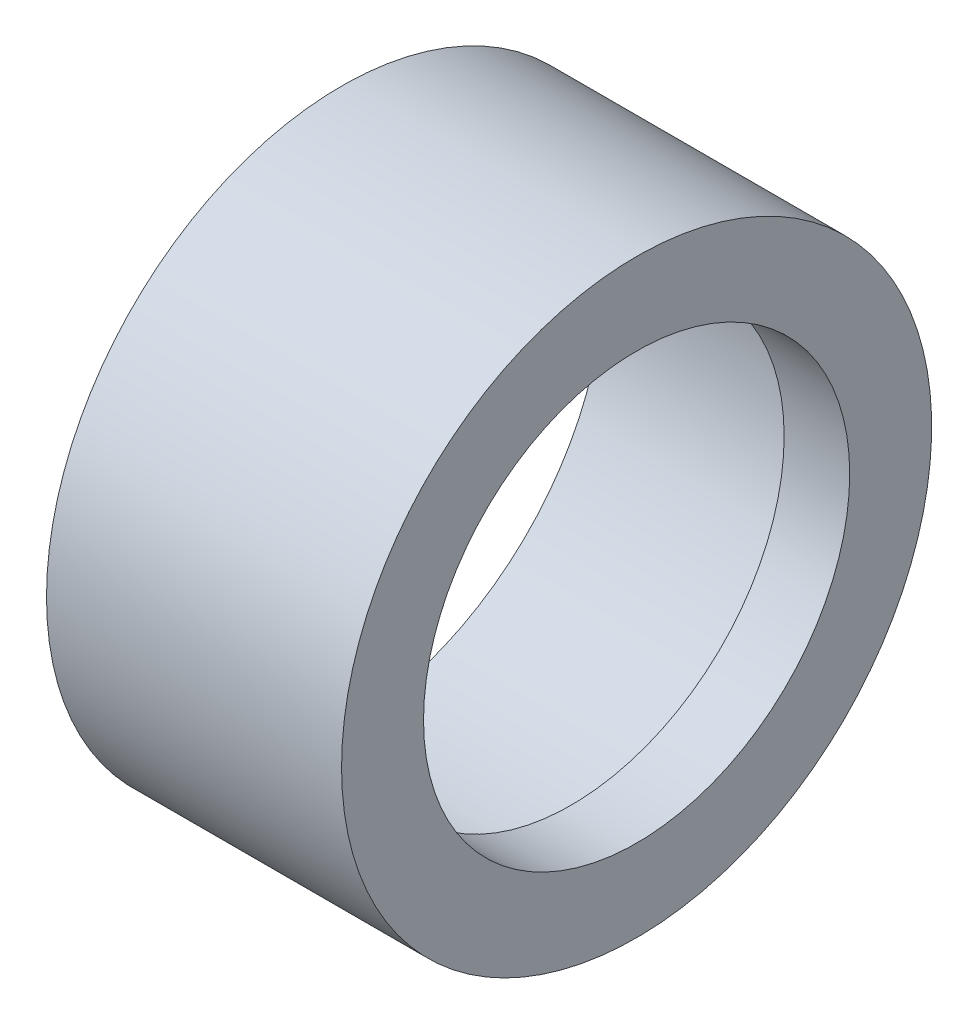
SolidWorks part; units mm, degrees
material "AISI Тип 316L нержавеющая сталь"
ref_plane "Спереди" through (0, 0, 0) normal (0, 0, 1) x (1, 0, 0)
ref_plane "Сверху" through (0, 0, 0) normal (0, 1, 0) x (1, 0, 0)
ref_plane "Справа" through (0, 0, 0) normal (1, 0, 0) x (0, 0, -1)
sketch "Эскиз1" plane through (0, 0, 0) normal (0, 0, 1) x (1, 0, 0)
  line L0 (0, 4) -> (3.5, 4)
  line L1 (3.5, 4) -> (3.5, 3.25)
  line L2 (3.5, 3.25) -> (4.5, 3.25)
  line L3 (4.5, 3.25) -> (4.5, 4.5)
  line L4 (4.5, 4.5) -> (0, 4.5)
  line L5 (0, 4.5) -> (0, 4)
  line L6 (0, 0) -> (5.6278, 0) construction
  dimension "D1" = 3.5
  dimension "D2" = 4.5
  dimension "D3" = 6.5
  dimension "D4" = 8
  dimension "D5" = 9
revolve "Повернуть1" add sketch "Эскиз1" angle 360 about L6
